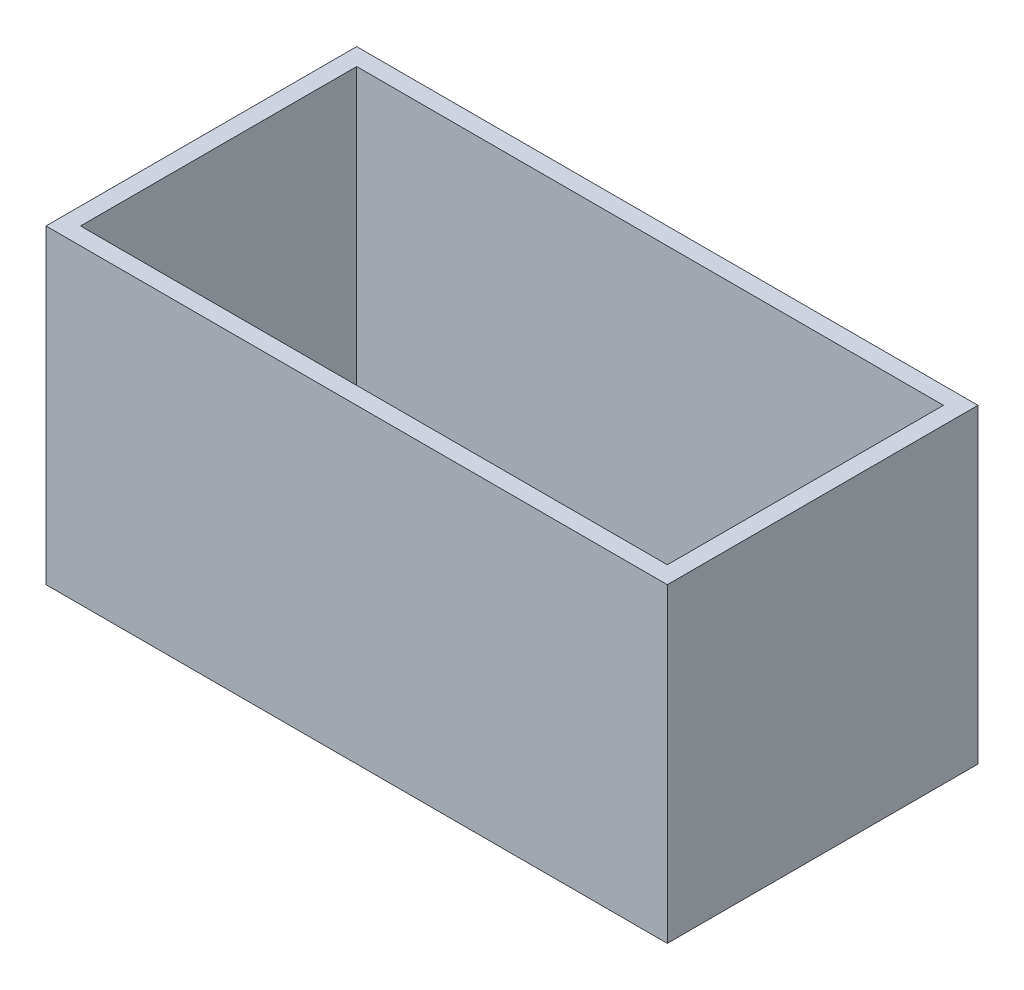
SolidWorks part; units mm, degrees
ref_plane "Front Plane" through (0, 0, 0) normal (0, 0, 1) x (1, 0, 0)
ref_plane "Top Plane" through (0, 0, 0) normal (0, 1, 0) x (1, 0, 0)
ref_plane "Right Plane" through (0, 0, 0) normal (1, 0, 0) x (0, 0, -1)
sketch "Sketch1" plane through (0, 0, 0) normal (0, 1, 0) x (1, 0, 0)
  line L1 (-18, -9) -> (18, -9)
  line L2 (-18, -9) -> (-18, 9)
  line L3 (-18, 9) -> (18, 9)
  line L4 (18, -9) -> (18, 9)
  line L5 (-18, -9) -> (18, 9) construction
  line L6 (-18, 9) -> (18, -9) construction
  point P0 (0, 0)
  dimension "D1" = 36
  dimension "D2" = 18
extrude "Boss-Extrude1" add sketch "Sketch1" along normal blind 18
shell "Shell1" thickness 1
equation "\"L\" = 18'lenth of a rib"
equation "\"D2@Sketch1\"=\"L\""
equation "\"D1@Sketch1\"=\"L\"*2"
equation "\"D1@Boss-Extrude1\"=\"L\""
